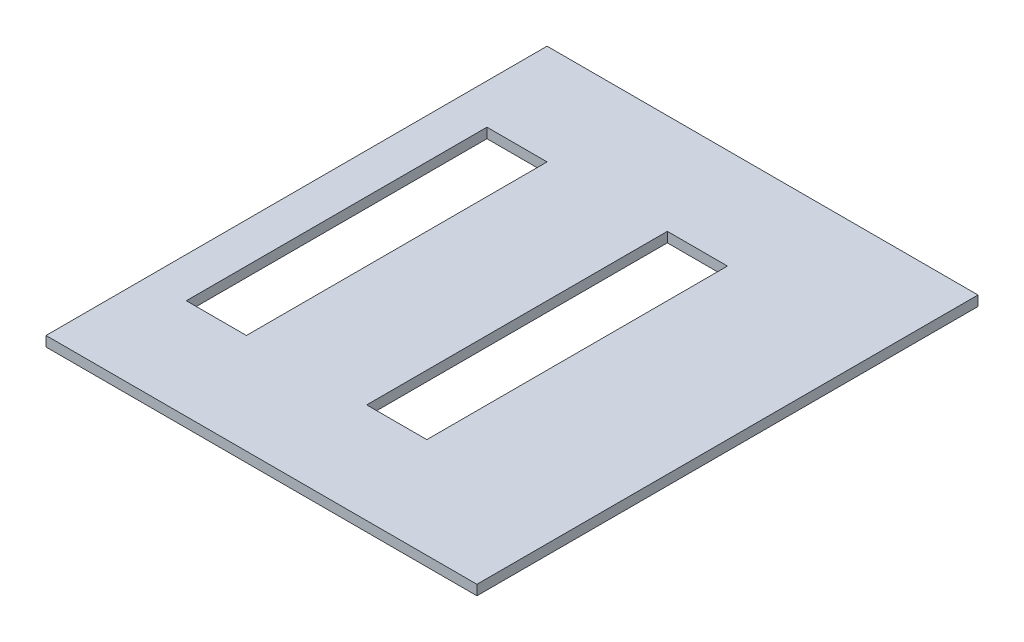
SolidWorks part; units mm, degrees
material "Polyurethane Foam Flexible"
ref_plane "Front Plane" through (0, 0, 0) normal (0, 0, 1) x (1, 0, 0)
ref_plane "Top Plane" through (0, 0, 0) normal (0, 1, 0) x (1, 0, 0)
ref_plane "Right Plane" through (0, 0, 0) normal (1, 0, 0) x (0, 0, -1)
sketch "Sketch1" plane through (0, 0, 0) normal (0, 1, 0) x (1, 0, 0)
  line L1 (-1092.2, 1270) -> (1092.2, 1270)
  line L2 (-1092.2, 1270) -> (-1092.2, -1270)
  line L3 (-1092.2, -1270) -> (1092.2, -1270)
  line L4 (1092.2, 1270) -> (1092.2, -1270)
  line L5 (-1092.2, 1270) -> (1092.2, -1270) construction
  line L6 (-1092.2, -1270) -> (1092.2, 1270) construction
  point P0 (0, 0)
  dimension "D1" = 2184.4
  dimension "D2" = 2540
extrude "Boss-Extrude1" add sketch "Sketch1" along normal blind 50.8
sketch "Sketch2" plane through (0, 50.8, 0) normal (0, 1, 0) x (1, 0, 0)
  line L1 (25.4, -762) -> (330.2, -762)
  line L2 (25.4, -762) -> (25.4, 762)
  line L3 (25.4, 762) -> (330.2, 762)
  line L4 (330.2, -762) -> (330.2, 762)
  line L5 (25.4, -762) -> (330.2, 762) construction
  line L6 (25.4, 762) -> (330.2, -762) construction
  line L7 (-889, -762) -> (-584.2, -762)
  line L8 (-889, -762) -> (-889, 762)
  line L9 (-889, 762) -> (-584.2, 762)
  line L10 (-584.2, -762) -> (-584.2, 762)
  line L11 (-889, -762) -> (-584.2, 762) construction
  line L12 (-889, 762) -> (-584.2, -762) construction
  line L13 (1092.2, 1270) -> (-1092.2, 1270) construction
  line L14 (1092.2, -1270) -> (1092.2, 1270) construction
  point P0 (177.8, 0)
  point P5 (-736.6, 0)
  dimension "D1" = 304.8
  dimension "D2" = 304.8
  dimension "D3" = 609.6
  dimension "D4" = 508
  dimension "D5" = 762
  dimension "D6" = 1524
extrude "Cut-Extrude1" cut sketch "Sketch2" against normal up to surface (50.8 mm away) up to face at (0, 0, 0)
